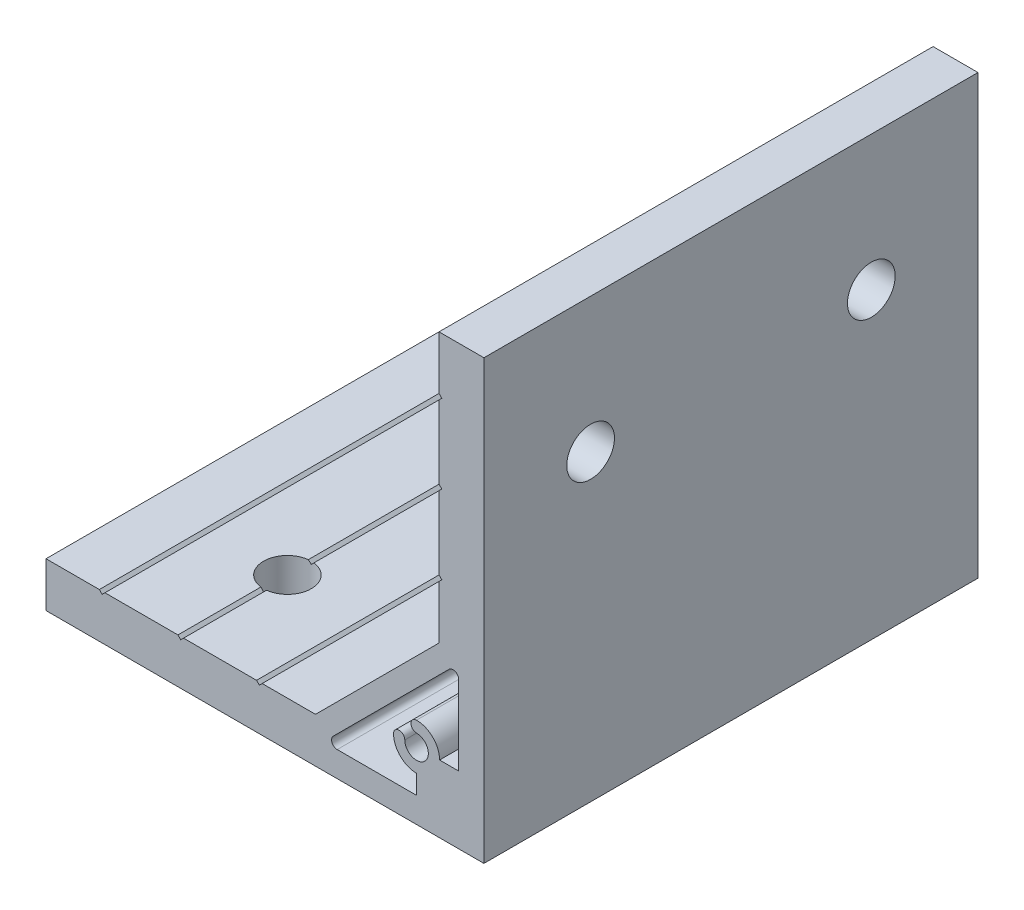
SolidWorks part; units mm, degrees
material "6063 T5"
ref_plane "Спереди" through (0, 0, 0) normal (0, 0, 1) x (1, 0, 0)
ref_plane "Сверху" through (0, 0, 0) normal (0, 1, 0) x (1, 0, 0)
ref_plane "Справа" through (0, 0, 0) normal (1, 0, 0) x (0, 0, -1)
sketch "Эскиз1" plane through (0, 0, 0) normal (0, 0, 1) x (1, 0, 0)
  line L0 (-78, 0) -> (0, 0)
  line L1 (0, 0) -> (0, 78)
  line L3 (-8, 53.5) -> (-8, 40.5)
  line L4 (-8, 40.5) -> (-7.5, 40)
  line L5 (-7.5, 40) -> (-8, 39.5)
  line L6 (-8, 39.5) -> (-8, 30)
  line L7 (-8, 30) -> (-30, 8)
  line L8 (-30, 8) -> (-39.5, 8)
  line L9 (-39.5, 8) -> (-40, 7.5)
  line L10 (-40, 7.5) -> (-40.5, 8)
  line L11 (-40.5, 8) -> (-53.5, 8)
  line L13 (-4.5, 12) -> (-4.5, 26.136)
  line L14 (-6.2071, 26.8431) -> (-26.8431, 6.2071)
  line L15 (-26.136, 4.5) -> (-12, 4.5)
  line L16 (-12, 4.5) -> (-12, 7.9)
  line L17 (-7.9, 12) -> (-4.5, 12)
  line L18 (-8, 53.5) -> (-7.5, 54)
  line L19 (-7.5, 54) -> (-8, 54.5)
  line L20 (-8, 54.5) -> (-8, 67.5)
  line L21 (-8, 67.5) -> (-7.5, 68)
  line L22 (-7.5, 68) -> (-8, 68.5)
  line L23 (-8, 68.5) -> (-8, 78)
  line L24 (-8, 78) -> (0, 78)
  line L25 (-53.5, 8) -> (-54, 7.5)
  line L26 (-54, 7.5) -> (-54.5, 8)
  line L27 (-54.5, 8) -> (-67.5, 8)
  line L28 (-67.5, 8) -> (-68, 7.5)
  line L29 (-68, 7.5) -> (-68.5, 8)
  line L30 (-68.5, 8) -> (-78, 8)
  line L31 (-78, 8) -> (-78, 0)
  arc A0 (-4.5, 26.136) -> (-6.2071, 26.8431) centre (-5.5, 26.136) ccw
  arc A1 (-26.8431, 6.2071) -> (-26.136, 4.5) centre (-26.136, 5.5) ccw
  arc A2 (-12, 7.9) -> (-16.1, 12) centre (-12, 12) cw
  arc A3 (-16.1, 12) -> (-14.1, 12) centre (-15.1, 12) cw
  arc A4 (-14.1, 12) -> (-12, 14.1) centre (-12, 12) ccw
  arc A5 (-12, 14.1) -> (-12, 16.1) centre (-12, 15.1) cw
  arc A6 (-12, 16.1) -> (-7.9, 12) centre (-12, 12) cw
  dimension "D6" = 4.2
  dimension "D7" = 1
  dimension "D9" = 1
  dimension "D2" = 8
  dimension "D3" = 135
  dimension "D4" = 12
  dimension "D5" = 12
  dimension "D8" = 30
  dimension "D10" = 3.5
  dimension "D11" = 4.5
  dimension "D12" = 40
  dimension "D13" = 1
  dimension "D14" = 54
  dimension "D15" = 68
  dimension "D16" = 78
extrude "Бобышка-Вытянуть1" add sketch "Эскиз1" along normal mid plane 88
sketch "Эскиз2" plane through (-8, 0, 0) normal (-1, 0, 0) x (0, 0, 1)
  line L1 (44, 54) -> (-44, 54) construction
  line L2 (-25, 54) -> (25, 54) construction
  circle A0 centre (-25, 54) radius 4.25
  circle A1 centre (25, 54) radius 4.25
  point P2 (0, 54)
  dimension "D1" = 8.5
  dimension "D2" = 50
extrude "Вырез-Вытянуть1" cut sketch "Эскиз2" against normal through all
sketch "Эскиз3" plane through (0, 8, 0) normal (0, 1, 0) x (1, 0, 0)
  line L1 (-54, -44) -> (-54, 44) construction
  line L2 (-54, 25) -> (-54, -25) construction
  circle A0 centre (-54, -25) radius 4.25
  circle A1 centre (-54, 25) radius 4.25
  point P2 (-54, 0)
  dimension "D1" = 8.5
  dimension "D2" = 50
extrude "Вырез-Вытянуть2" cut sketch "Эскиз3" against normal through all
